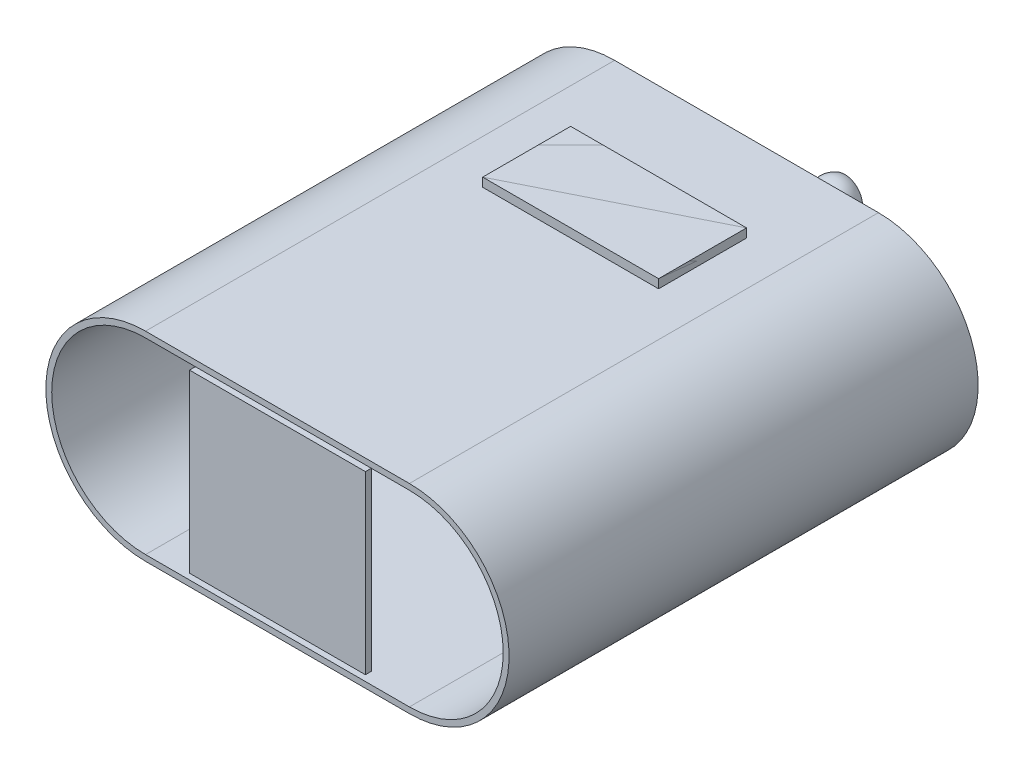
SolidWorks part; units mm, degrees
other "COLL.BOX-Boss-Extrude7"
other "COLL.BOX-Boss-Extrude5"
other "COLL.BOX-Boss-Extrude4"
other "COLL.BOX-Boss-Extrude3"
other "COLL.BOX-Boss-Extrude8"
ref_plane "Front Plane" through (0, 0, 0) normal (0, 0, 1) x (1, 0, 0)
ref_plane "Top Plane" through (0, 0, 0) normal (0, 1, 0) x (1, 0, 0)
ref_plane "Right Plane" through (0, 0, 0) normal (1, 0, 0) x (0, 0, -1)
sketch "Sketch1" plane through (0, 0, 0) normal (0, 0, 1) x (1, 0, 0)
  line L1 (-22.5, -17) -> (22.5, -17)
  line L2 (-22.5, -17) -> (-22.5, 17)
  line L3 (-22.5, 17) -> (22.5, 17)
  line L4 (22.5, -17) -> (22.5, 17)
  line L5 (-22.5, -17) -> (22.5, 17) construction
  line L6 (-22.5, 17) -> (22.5, -17) construction
  arc A0 (-22.5, 17) -> (-22.5, -17) centre (-22.5, 0) ccw
  arc A1 (22.5, 17) -> (22.5, -17) centre (22.5, 0) cw
  point P0 (0, 0)
  dimension "D1" = 34
  dimension "D2" = 45
extrude "Boss-Extrude1" add sketch "Sketch1" along normal blind 80 contours L2 A0 | L1 L4 L3 L2 | A1 L4
shell "Shell1" thickness 1
sketch "Sketch2" plane through (0, -17, 0) normal (0, -1, 0) x (1, 0, 0)
  line L0 (-22.5, 0) -> (22.5, 0) construction
  line L1 (-15, 30) -> (15, 30)
  line L2 (-15, 30) -> (-15, 15)
  line L3 (-15, 15) -> (15, 15)
  line L4 (15, 30) -> (15, 15)
  dimension "D1" = 15
  dimension "D2" = 30
  dimension "D3" = 15
  dimension "D4" = 15
extrude "Boss-Extrude2" add sketch "Sketch2" along normal blind 1.5
mirror "Mirror1" about plane through (0, 0, 0) normal (0, 1, 0) of "Boss-Extrude2"
sketch "Sketch3" plane through (0, 18.5, 0) normal (0, 1, 0) x (1, 0, 0)
  line L1 (-15, -15) -> (15, -15)
  line L2 (-15, -15) -> (-15, -30)
  line L3 (-15, -30) -> (15, -30)
  line L4 (15, -15) -> (15, -30)
extrude "Boss-Extrude3" add sketch "Sketch3" against normal blind 1.5 separate body
sketch "Sketch4" plane through (0, -18.5, 0) normal (0, -1, 0) x (1, 0, 0)
  line L1 (-15, 30) -> (15, 30)
  line L2 (-15, 30) -> (-15, 15)
  line L3 (-15, 15) -> (15, 15)
  line L4 (15, 30) -> (15, 15)
extrude "Boss-Extrude4" add sketch "Sketch4" against normal blind 1.5 separate body
sketch "Sketch5" plane through (0, 0, 0) normal (0, 0, -1) x (-1, 0, 0)
  line L1 (-22.5, -16) -> (22.5, -16)
  line L2 (-22.5, -16) -> (-22.5, 16)
  line L3 (-22.5, 16) -> (22.5, 16)
  line L4 (22.5, -16) -> (22.5, 16)
  line L5 (-22.5, -16) -> (22.5, 16) construction
  line L6 (-22.5, 16) -> (22.5, -16) construction
  point P0 (0, 0)
  dimension "D1" = 32
  dimension "D2" = 45
extrude "Boss-Extrude5" add sketch "Sketch5" against normal blind 1 separate body
sketch "Sketch6" plane through (0, 0, 0) normal (0, 0, -1) x (-1, 0, 0)
  circle A0 centre (0, 0) radius 1.25
  dimension "D1" = 2.5
extrude "Boss-Extrude6" add sketch "Sketch6" along normal blind 15
ref_plane "Plane1" through (0, 0, -15) normal (0, 0, -1) x (-1, 0, 0)
ref_point "Point1"
sketch "Sketch7" plane through (0, 0, -15) normal (0, 0, -1) x (-1, 0, 0)
  line L0 (-3.5, 0) -> (3.5, 0)
  arc A0 (3.5, 0) -> (-3.5, 0) centre (0, 0) ccw
  dimension "D1" = 3.5
revolve "Revolve1" add sketch "Sketch7" angle 360 about L0
sketch "Sketch8" plane through (0, 0, -15) normal (0, 0, -1) x (-1, 0, 0)
  line L0 (0, 2.5) -> (0, -2.5)
  arc A0 (0, 2.5) -> (0, -2.5) centre (0, 0) cw
  dimension "D1" = 2.5
revolve "Cut-Revolve1" cut sketch "Sketch8" angle 360 about L0
ref_plane "Plane2" through (0, 0, -16.75) normal (0, 0, -1) x (-1, 0, 0)
sketch "Sketch9" plane through (0, 0, -16.75) normal (0, 0, -1) x (-1, 0, 0)
  circle A0 centre (0, 0) radius 3.5
extrude "Cut-Extrude1" cut sketch "Sketch9" along normal through all
sketch "Sketch10" plane through (0, 0, 0) normal (0, 0, -1) x (-1, 0, 0)
  line L1 (-22.5, -16) -> (22.5, -16)
  line L2 (-22.5, -16) -> (-22.5, 16)
  line L3 (-22.5, 16) -> (22.5, 16)
  line L4 (22.5, -16) -> (22.5, 16)
  line L5 (-22.5, -16) -> (22.5, 16) construction
  line L6 (-22.5, 16) -> (22.5, -16) construction
  point P0 (0, 0)
  dimension "D1" = 32
  dimension "D2" = 45
extrude "Boss-Extrude7" add sketch "Sketch10" against normal blind 1 separate body
sketch "Sketch11" plane through (0, 0, 80) normal (0, 0, 1) x (1, 0, 0)
  line L1 (-15, -15) -> (15, -15)
  line L2 (-15, -15) -> (-15, 15)
  line L3 (-15, 15) -> (15, 15)
  line L4 (15, -15) -> (15, 15)
  line L5 (-15, -15) -> (15, 15) construction
  line L6 (-15, 15) -> (15, -15) construction
  point P0 (0, 0)
  dimension "D1" = 30
extrude "Boss-Extrude8" add sketch "Sketch11" against normal blind 1 separate body
